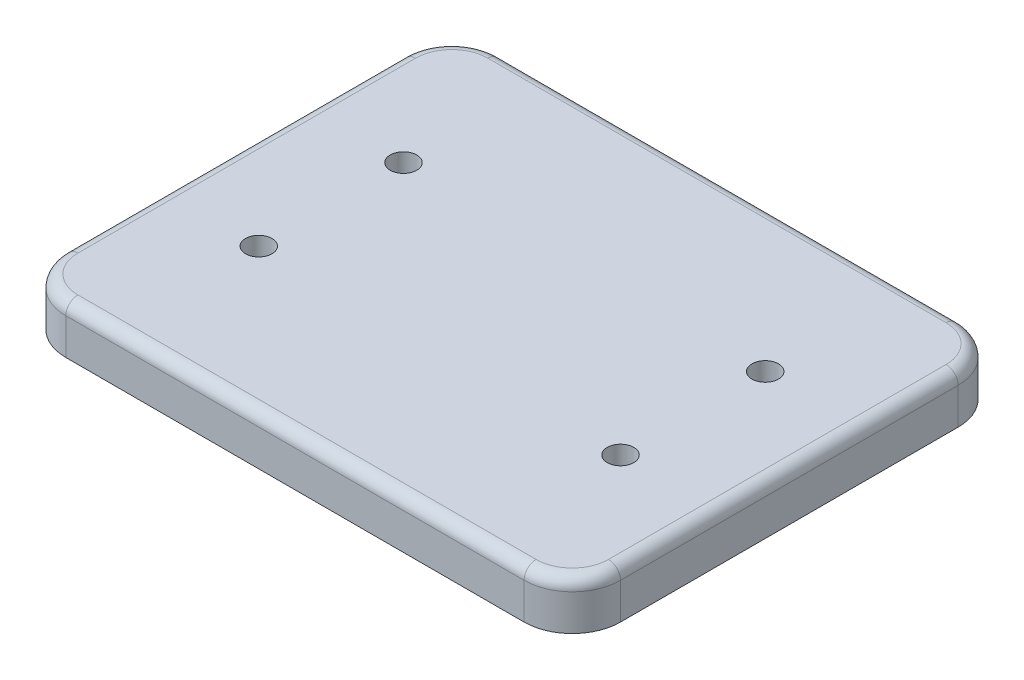
SolidWorks part; units mm, degrees
ref_plane "Front Plane" through (0, 0, 0) normal (0, 0, 1) x (1, 0, 0)
ref_plane "Top Plane" through (0, 0, 0) normal (0, 1, 0) x (1, 0, 0)
ref_plane "Right Plane" through (0, 0, 0) normal (1, 0, 0) x (0, 0, -1)
sketch "Sketch1" plane through (0, 0, 0) normal (0, 1, 0) x (1, 0, 0)
  line L0 (115, 90) -> (-115, -90) construction
  line L1 (115, -90) -> (-115, 90) construction
  line L2 (-115, 70) -> (-115, -70)
  line L3 (-95, -90) -> (95, -90)
  line L4 (115, -70) -> (115, 70)
  line L5 (95, 90) -> (-95, 90)
  arc A0 (-115, -70) -> (-95, -90) centre (-95, -70) ccw
  arc A1 (115, -70) -> (95, -90) centre (95, -70) cw
  arc A2 (115, 70) -> (95, 90) centre (95, 70) ccw
  arc A3 (-95, 90) -> (-115, 70) centre (-95, 70) ccw
  point P4 (0, 0)
  point P8 (0, 0)
  point P9 (-117.838, 71.1875)
  dimension "D3" = 20
  dimension "D1" = 230
  dimension "D2" = 180
extrude "Boss-Extrude1" add sketch "Sketch1" along normal blind 20
fillet "Fillet1" radius 5 8 edges at (-109.1421, 20, 84.1421) (-115, 20, 0) (-109.1421, 20, -84.1421) (0, 20, -90) (109.1421, 20, -84.1421) (115, 20, 0) (109.1421, 20, 84.1421) (0, 20, 90)
sketch "Sketch2" plane through (0, 20, 0) normal (0, 1, 0) x (1, 0, 0)
  circle A0 centre (-75, 30) radius 5.5
  circle A1 centre (75, 30) radius 5.5
  point P4 (0, 0)
  dimension "D4" = 11
  dimension "D1" = 30
  dimension "D2" = 75
  dimension "D3" = 75
extrude "Cut-Extrude1" cut sketch "Sketch2" against normal through all
sketch "Sketch3" plane through (0, 0, 0) normal (0, -1, 0) x (1, 0, 0)
  circle A0 centre (-75, -30) radius 9
  circle A1 centre (75, -30) radius 9
  dimension "D1" = 18
extrude "Cut-Extrude2" cut sketch "Sketch3" against normal blind 11
mirror "Mirror1" about plane through (0, 0, 0) normal (0, 0, 1) of "Cut-Extrude1", "Cut-Extrude2"
